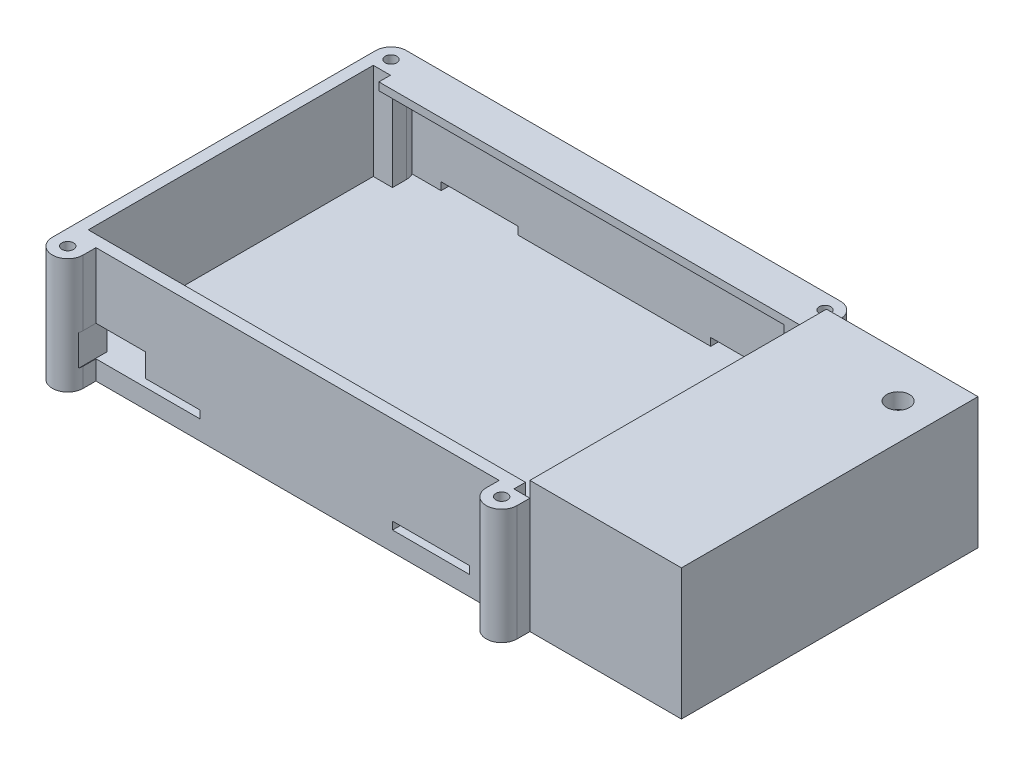
SolidWorks part; units mm, degrees
ref_plane "Front Plane" through (0, 0, 0) normal (0, 0, 1) x (1, 0, 0)
ref_plane "Top Plane" through (0, 0, 0) normal (0, 1, 0) x (1, 0, 0)
ref_plane "Right Plane" through (0, 0, 0) normal (1, 0, 0) x (0, 0, -1)
sketch "Sketch1" plane through (0, 0, 0) normal (0, 1, 0) x (1, 0, 0)
  line L1 (0, 0) -> (-160, 0)
  line L2 (0, 0) -> (0, -77)
  line L3 (0, -77) -> (-160, -77)
  line L4 (-160, 0) -> (-160, -77)
  dimension "D1" = 160
  dimension "D2" = 77
extrude "Boss-Extrude1" add sketch "Sketch1" along normal blind 5
sketch "Sketch2" plane through (0, 5, 0) normal (0, 1, 0) x (1, 0, 0)
  line L1 (-160, 0) -> (-157, 0)
  line L2 (-160, 0) -> (-160, -77)
  line L3 (-160, -77) -> (0, -77)
  line L4 (0, 0) -> (0, -77)
  line L5 (-3, -3) -> (-3, -74)
  line L6 (-157, -74) -> (-3, -74)
  line L7 (-157, 0) -> (-157, -74)
  line L10 (-47.4, 0) -> (-47.4, -3)
  line L12 (-47.4, 0) -> (0, 0)
  line L13 (-160, 0) -> (0, 0) construction
  line L14 (-47.4, -3) -> (-3, -3)
  line L15 (-157, -3) -> (-3, -3) construction
  line L16 (0, 0) -> (-160, 0) construction
  line L17 (-157, -3) -> (-157, -74) construction
  dimension "D2" = 47.4
  dimension "D3" = 3
  dimension "D1" = 3
extrude "Boss-Extrude2" add sketch "Sketch2" along normal blind 25 contours L1 L2 L3 L4 L12 L10 L14 L5 L6 L7
sketch "Sketch3" plane through (0, 0, 0) normal (0, -1, 0) x (1, 0, 0)
  line L0 (-160, 77) -> (0, 77) construction
  line L1 (-160, 77) -> (-152.006, 77)
  line L2 (-160, 77) -> (-160, 80.3267)
  line L4 (-152.006, 77) -> (-152.006, 80.3267)
  line L6 (-47.3337, 80.3267) -> (-47.3337, 77)
  line L7 (-47.3337, 77) -> (-39.3418, 77)
  line L8 (-39.3418, 80.3267) -> (-39.3418, 77)
  line L19 (0, 0) -> (-160, 0) construction
  line L20 (-160, 0) -> (-152.006, 0)
  line L21 (-160, 0) -> (-160, -3.6133)
  line L23 (-152.006, 0) -> (-152.006, -3.6133)
  line L25 (-47.3337, -3.6133) -> (-47.3337, 0)
  line L26 (-47.3337, 0) -> (-39.3418, 0)
  line L27 (-39.3418, -3.6133) -> (-39.3418, 0)
  arc A0 (-152.006, 80.3267) -> (-160, 80.3267) centre (-156.003, 80.3267) ccw
  arc A4 (-39.3418, 80.3267) -> (-47.3337, 80.3267) centre (-43.3378, 80.3267) ccw
  circle A5 centre (-43.3378, 80.3267) radius 1.5
  circle A6 centre (-156.003, 80.3267) radius 1.5
  arc A7 (-160, -3.6133) -> (-152.006, -3.6133) centre (-156.003, -3.6133) ccw
  circle A8 centre (-156.003, -3.6133) radius 1.5
  arc A9 (-47.3337, -3.6133) -> (-39.3418, -3.6133) centre (-43.3378, -3.6133) ccw
  circle A10 centre (-43.3378, -3.6133) radius 1.5
  dimension "D2" = 3.997
  dimension "D4" = 3.9959
  dimension "D5" = 3
  dimension "D7" = 3.997
  dimension "D8" = 3
  dimension "D9" = 3
  dimension "D10" = 3.9959
  dimension "D11" = 3
  dimension "D1" = 3.3267
  dimension "D3" = 3.6133
  dimension "D6" = 7.9918
  dimension "D12" = 112.6652
  dimension "D13" = 3.6133
  dimension "D14" = 3.997
  dimension "D15" = 112.6652
  dimension "D16" = 3.997
  dimension "D17" = 7.994
  dimension "D18" = 3.3267
  dimension "D19" = 7.9918
  dimension "D20" = 3.6133
extrude "Boss-Extrude3" add sketch "Sketch3" against normal up to surface (30 mm away) contours L6 L7 L8 A4 | A0 L2 L1 L4 | A9 L27 L26 L25 | A10 | L21 A7 L23 L20 | A8 | A6 | A5 up to face at (-73.48, 30, 30.8)
sketch "Sketch5" plane through (0, 30, 0) normal (0, 1, 0) x (1, 0, 0)
  line L1 (-39.3418, 0) -> (0, 0)
  line L2 (-39.3418, 0) -> (-39.3418, -77)
  line L3 (-39.3418, -77) -> (0, -77)
  line L4 (0, 0) -> (0, -77)
  circle A0 centre (-9.3881, -11.3566) radius 2.9474
extrude "Boss-Extrude5" add sketch "Sketch5" along normal blind 4 from surface at 0 starting at face at (-76.7966, 30, 34.9479)
sketch "Sketch8" plane through (0, 0, 0) normal (0, -1, 0) x (1, 0, 0)
  line L0 (-160, 0) -> (-160, -3.6133)
  line L1 (-43.3378, 0) -> (-156.003, 0)
  line L3 (-43.3378, -7.6093) -> (-156.003, -7.6093)
  line L5 (-160, -3.6133) -> (-160, 80.3267) construction
  line L9 (-156.003, -7.6093) -> (-156.003, 0)
  line L13 (-43.3378, 0) -> (-43.3378, -7.6093)
  arc A0 (-47.3337, -3.6133) -> (-39.3418, -3.6133) centre (-43.3378, -3.6133) ccw construction
  dimension "D1" = 3.997
  dimension "D2" = 3.6133
extrude "Boss-Extrude6" add sketch "Sketch8" against normal up to surface (5 mm away)
sketch "Sketch9" plane through (0, 5, 0) normal (0, 1, 0) x (1, 0, 0)
  line L1 (-155.9108, 7.6093) -> (-43.3378, 7.6093)
  line L2 (-155.9108, 7.6093) -> (-155.9108, 5.6093)
  line L3 (-155.9108, 5.6093) -> (-43.3378, 5.6093)
  line L4 (-43.3378, 7.6093) -> (-43.3378, 5.6093)
  dimension "D1" = 2
  dimension "D2" = 112.573
extrude "Boss-Extrude7" add sketch "Sketch9" along normal up to surface (25 mm away) up to face at (-43.3378, 30, 81.8267)
sketch "Sketch7" plane through (0, 0, 0) normal (0, 0, -1) x (-1, 0, 0)
  line L1 (139.1418, 13) -> (152.1418, 13)
  line L2 (139.1418, 13) -> (139.1418, 5)
  line L3 (139.1418, 5) -> (152.1418, 5)
  line L4 (152.1418, 13) -> (152.1418, 5)
  line L5 (39.3418, 30) -> (39.3418, 0) construction
  line L6 (43.3378, 30) -> (155.9108, 30) construction
  dimension "D1" = 17
  dimension "D2" = 99.8
  dimension "D3" = 8
  dimension "D4" = 13
extrude "Cut-Extrude2" cut sketch "Sketch7" against normal blind 119 from surface at -74 starting at face at (-71.8684, 20, 74)
sketch "Sketch6" plane through (0, 0, 77) normal (0, 0, 1) x (1, 0, 0)
  line L0 (-160, 30) -> (-160, 0) construction
  line L1 (-145, 5) -> (-125, 5)
  line L2 (-145, 5) -> (-145, 7)
  line L3 (-145, 7) -> (-125, 7)
  line L4 (-125, 5) -> (-125, 7)
  line L5 (-75, 5) -> (-55, 5)
  line L6 (-75, 5) -> (-75, 7)
  line L7 (-75, 7) -> (-55, 7)
  line L8 (-55, 5) -> (-55, 7)
  line L9 (-152.006, 0) -> (-47.3337, 0) construction
  dimension "D1" = 15
  dimension "D2" = 20
  dimension "D3" = 20
  dimension "D4" = 5
  dimension "D5" = 2
  dimension "D6" = 50
extrude "Cut-Extrude1" cut sketch "Sketch6" against normal blind 179
sketch "Sketch10" plane through (0, 30, 0) normal (0, 1, 0) x (1, 0, 0)
  line L0 (-157, -74) -> (-39.3418, -74) construction
  line L1 (-39.4918, -77) -> (-43.4918, -77)
  line L2 (-39.4918, -77) -> (-39.4918, -74)
  line L3 (-39.4918, -74) -> (-43.4918, -74)
  line L4 (-43.4918, -77) -> (-43.4918, -74)
  line L6 (-39.3418, -80.3267) -> (-39.3418, -77) construction
  dimension "D1" = 4
  dimension "D2" = 0.15
extrude "Cut-Extrude3" cut sketch "Sketch10" against normal blind 7
sketch "Sketch11" plane through (0, 0, -5.6093) normal (0, 0, 1) x (1, 0, 0)
  line L0 (-46.7995, 30) -> (-46.7995, 5) construction
  line L1 (-152.54, 30) -> (-46.7995, 30)
  line L2 (-152.54, 30) -> (-152.54, 28)
  line L3 (-152.54, 28) -> (-46.7995, 28)
  line L4 (-46.7995, 30) -> (-46.7995, 28)
  dimension "D1" = 2
extrude "Boss-Extrude8" add sketch "Sketch11" along normal up to surface (8.6093 mm away) up to face at (-28.0284, 20, 3)
